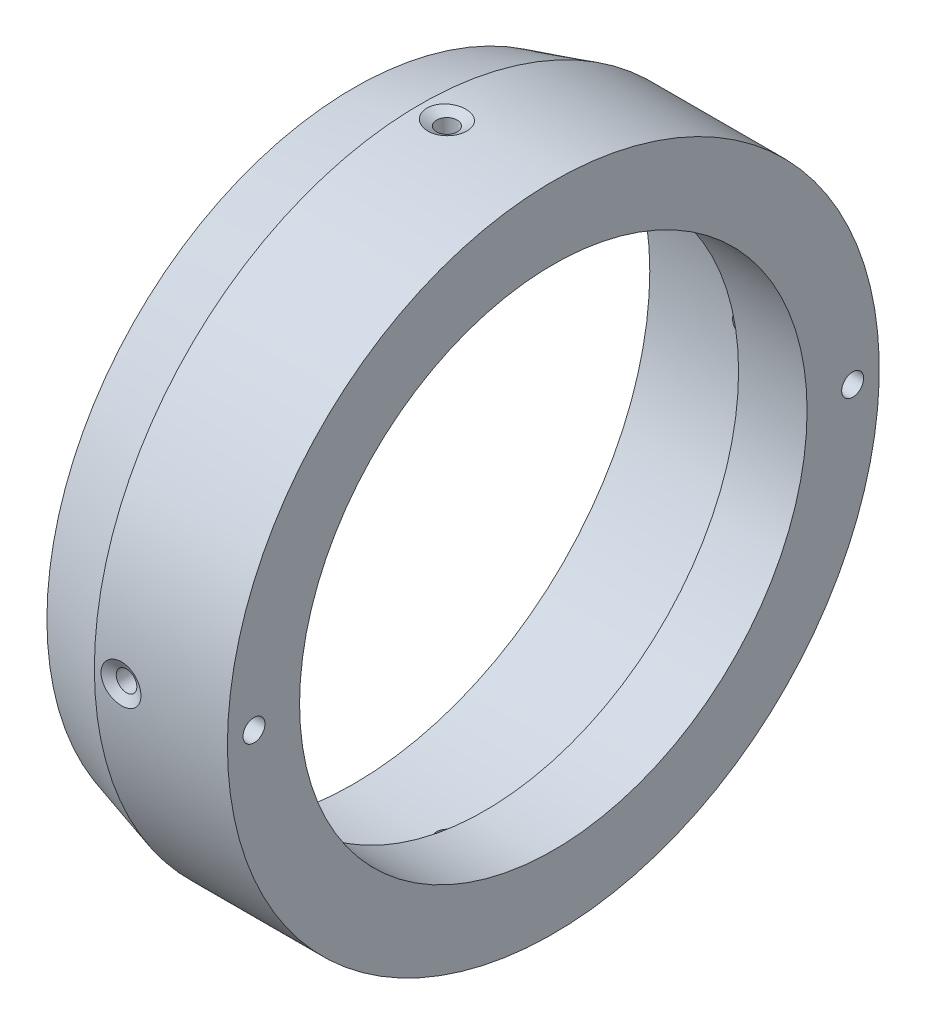
SolidWorks part; units mm, degrees
material "AISI 1020"
ref_plane "Plan de face" through (0, 0, 0) normal (0, 0, 1) x (1, 0, 0)
ref_plane "Plan de dessus" through (0, 0, 0) normal (0, 1, 0) x (1, 0, 0)
ref_plane "Plan de droite" through (0, 0, 0) normal (1, 0, 0) x (0, 0, -1)
sketch "Esquisse1" plane through (0, 0, 0) normal (0, 0, 1) x (1, 0, 0)
  line L0 (-37.5476, 0) -> (74.2848, 0) construction
  line L1 (0, 49) -> (0, 38.15)
  line L2 (0, 38.15) -> (-10.3, 38.15)
  line L5 (-10.3, 38.15) -> (-10.3, 44.5)
  line L6 (-10.3, 44.5) -> (-30, 44.5)
  line L7 (-30, 44.5) -> (-30, 49)
  line L8 (-30, 49) -> (0, 49)
  dimension "D1" = 98
  dimension "D2" = 89
  dimension "D3" = 30
  dimension "D4" = 76.3
  dimension "D5" = 10.3
revolve "Révolution1" add sketch "Esquisse1" angle 360 about L0
chamfer "Chanfrein1" distance 10 angle 16 1 edges at (-30, 0, 49)
hole_wizard "Trou taraudé M41" positions "Esquisse4" profile "Esquisse6" tap size "M4" standard "ISO"
sketch "Esquisse4" plane through (0, 0, 0) normal (1, 0, 0) x (0, 0, -1)
  line L0 (0, 0) -> (52.8256, 0) construction
  point P0 (45, 0)
  dimension "D1" = 45
sketch "Esquisse6" plane through (0, 0, -45) normal (0, 1, 0) x (0, 0, -1)
  line L0 (0, 0) -> (0, 7.9914)
  line L1 (0, 7.9914) -> (1.65, 7)
  line L2 (1.65, 7) -> (1.65, 0)
  line L5 (1.65, 0) -> (0, 0)
  line L10 (0, 7.9914) -> (-1.65, 7) construction
  line L11 (0, -6.35) -> (0, 107.95) construction
  dimension "Diamètre du trou pour taraudage" = 3.3
  dimension "Profondeur du trou pour taraudage" = 7
  dimension "Angle de pointe" = 118
cosmetic thread "Filetage de perçage1" parameters "D1"=6, "D2"=4
pattern_circular "Répétition circulaire1" count 2 over 360 about axis through (0, 0, 0) along (1, 0, 0) of "Trou taraudé M41"
hole_wizard "Dégagement M2.51" positions "Esquisse3D1" profile "Esquisse8" hole size "M2.5" standard "ISO"
sketch3d "Esquisse3D1"
  line L1 (0, 0, 0) -> (0, 0, -77.9381) construction
  line L5 (-25.8884, 0, -49) -> (0, 0, -49) construction
  point P0 (-16, 0, -49)
  dimension "D1" = 16
sketch "Esquisse8" plane through (-16, 0, -49) normal (1, 0, 0) x (0, 1, 0)
  line L0 (0, 0) -> (0, 20.9313)
  line L1 (0, 20.9313) -> (1.55, 20)
  line L2 (1.55, 20) -> (1.55, 0.8372)
  line L3 (1.55, 0.8372) -> (3, 0)
  line L5 (3, 0) -> (0, 0)
  line L6 (-1.55, 0.8372) -> (-3, 0) construction
  line L10 (0, 20.9313) -> (-1.55, 20) construction
  line L11 (0, -6.35) -> (0, 107.95) construction
  dimension "Diamètre du perçage" = 3.1
  dimension "Profondeur du perçage" = 20
  dimension "Diamètre du fraisage entrant" = 6
  dimension "Angle du fraisage entrant" = 120
  dimension "Angle de pointe" = 118
pattern_circular "Répétition circulaire2" count 4 over 360 about axis through (0, 0, 0) along (-1, 0, 0) of "Dégagement M2.51"
